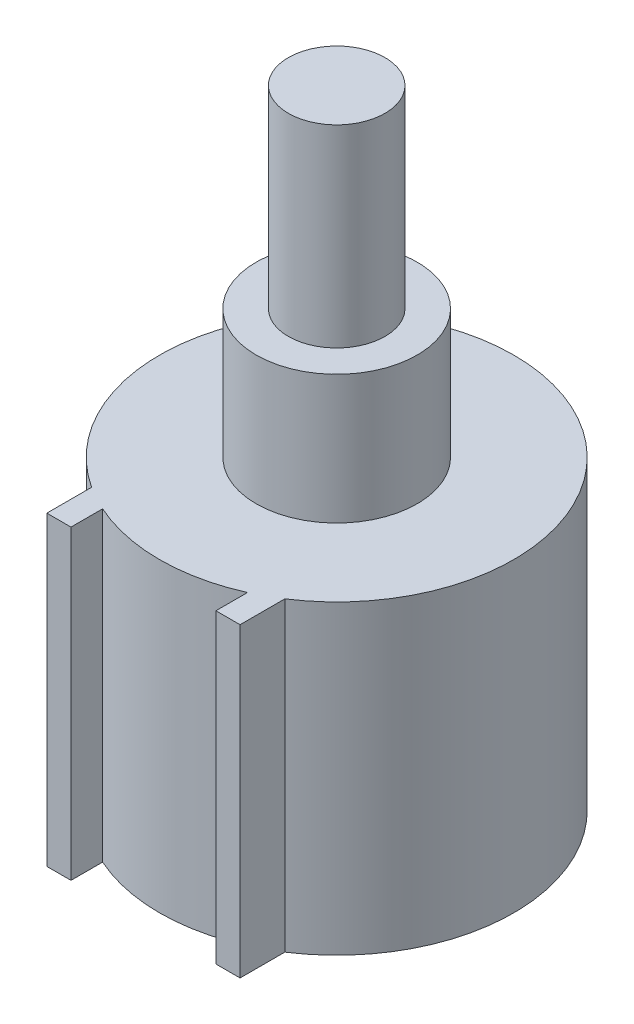
SolidWorks part; units mm, degrees
ref_plane "Front Plane" through (0, 0, 0) normal (0, 0, 1) x (1, 0, 0)
ref_plane "Top Plane" through (0, 0, 0) normal (0, 1, 0) x (1, 0, 0)
ref_plane "Right Plane" through (0, 0, 0) normal (1, 0, 0) x (0, 0, -1)
sketch "Sketch1" plane through (0, 0, 0) normal (0, 1, 0) x (1, 0, 0)
  line L1 (-6, -12) -> (-4.5, -12)
  line L2 (-6, -12) -> (-6, -9.2195)
  line L4 (-4.5, -12) -> (-4.5, -10.0374)
  line L5 (4.5, -12) -> (6, -12)
  line L6 (4.5, -12) -> (4.5, -10.0374)
  line L8 (6, -12) -> (6, -9.2195)
  arc A0 (-4.5, -10.0374) -> (4.5, -10.0374) centre (0, 0) ccw
  arc A1 (6, -9.2195) -> (-6, -9.2195) centre (0, 0) ccw
  dimension "D1" = 22
  dimension "D2" = 12
  dimension "D3" = 9
  dimension "D4" = 4.5
  dimension "D5" = 1.5
extrude "Boss-Extrude1" add sketch "Sketch1" along normal blind 19
sketch "Sketch2" plane through (0, 19, 0) normal (0, 1, 0) x (1, 0, 0)
  circle A0 centre (0, 0) radius 5
  dimension "D1" = 10
extrude "Boss-Extrude2" add sketch "Sketch2" along normal blind 8
sketch "Sketch3" plane through (0, 27, 0) normal (0, 1, 0) x (1, 0, 0)
  circle A0 centre (0, 0) radius 3
  dimension "D1" = 6
extrude "Boss-Extrude3" add sketch "Sketch3" along normal blind 12
